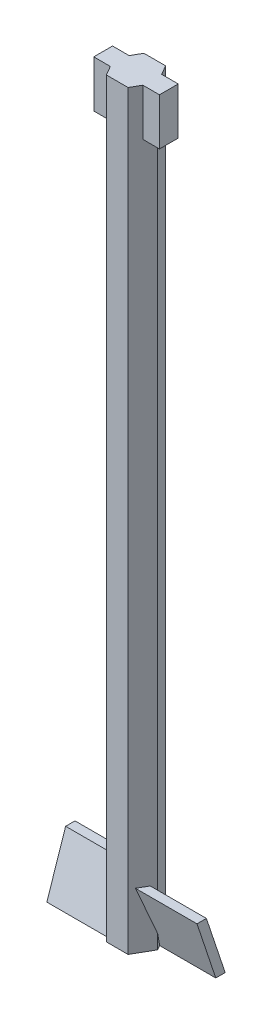
SolidWorks part; units mm, degrees
ref_plane "Front Plane" through (0, 0, 0) normal (0, 0, 1) x (1, 0, 0)
ref_plane "Top Plane" through (0, 0, 0) normal (0, 1, 0) x (1, 0, 0)
ref_plane "Right Plane" through (0, 0, 0) normal (1, 0, 0) x (0, 0, -1)
sketch "Sketch1" plane through (0, 0, 0) normal (0, 1, 0) x (1, 0, 0)
  line L1 (-1.1547, 2) -> (-2.3094, 0)
  line L2 (-2.3094, 0) -> (-1.1547, -2)
  line L3 (-1.1547, -2) -> (1.1547, -2)
  line L4 (1.1547, -2) -> (2.3094, 0)
  line L5 (2.3094, 0) -> (1.1547, 2)
  line L6 (1.1547, 2) -> (-1.1547, 2)
  circle A1 centre (0, 0) radius 2 construction
extrude "Boss-Extrude1" add sketch "Sketch1" along normal blind 80
sketch "Sketch2" plane through (0, 80, 0) normal (0, 1, 0) x (1, 0, 0)
  line L1 (-3.5, 1) -> (3.5, 1)
  line L2 (-3.5, 1) -> (-3.5, -1)
  line L3 (-3.5, -1) -> (3.5, -1)
  line L4 (3.5, 1) -> (3.5, -1)
  line L5 (-3.5, 1) -> (3.5, -1) construction
  line L6 (-3.5, -1) -> (3.5, 1) construction
  point P0 (0, 0)
  dimension "D1" = 2
  dimension "D2" = 7
extrude "Boss-Extrude2" add sketch "Sketch2" against normal blind 5
sketch "Sketch3" plane through (0, 0, 0) normal (1, 0, 0) x (0, 0, -1)
  line L0 (-1.5, 6) -> (-0.5, 6)
  line L2 (1.5, 0) -> (0.5, 0)
  line L4 (-1.5, 6) -> (0.5, 0)
  line L5 (-0.5, 6) -> (1.5, 0)
  dimension "D1" = 1
  dimension "D2" = 1
  dimension "D3" = 6
extrude "Boss-Extrude3" add sketch "Sketch3" along normal blind 8
sketch "Sketch4" plane through (0, 0, 0) normal (1, 0, 0) x (0, 0, -1)
  line L0 (1.5, 6) -> (0.5, 6)
  line L4 (-1.5, 0) -> (-0.5, 0)
  line L5 (1.5, 6) -> (-0.5, 0)
  line L6 (0.5, 6) -> (-1.5, 0)
  dimension "D1" = 1
  dimension "D2" = 6
  dimension "D3" = 1
extrude "Boss-Extrude4" add sketch "Sketch4" against normal blind 8
ref_plane "Plane1" through (0, 0, 0) normal (1, 0, 0) x (0, 0, -1)
